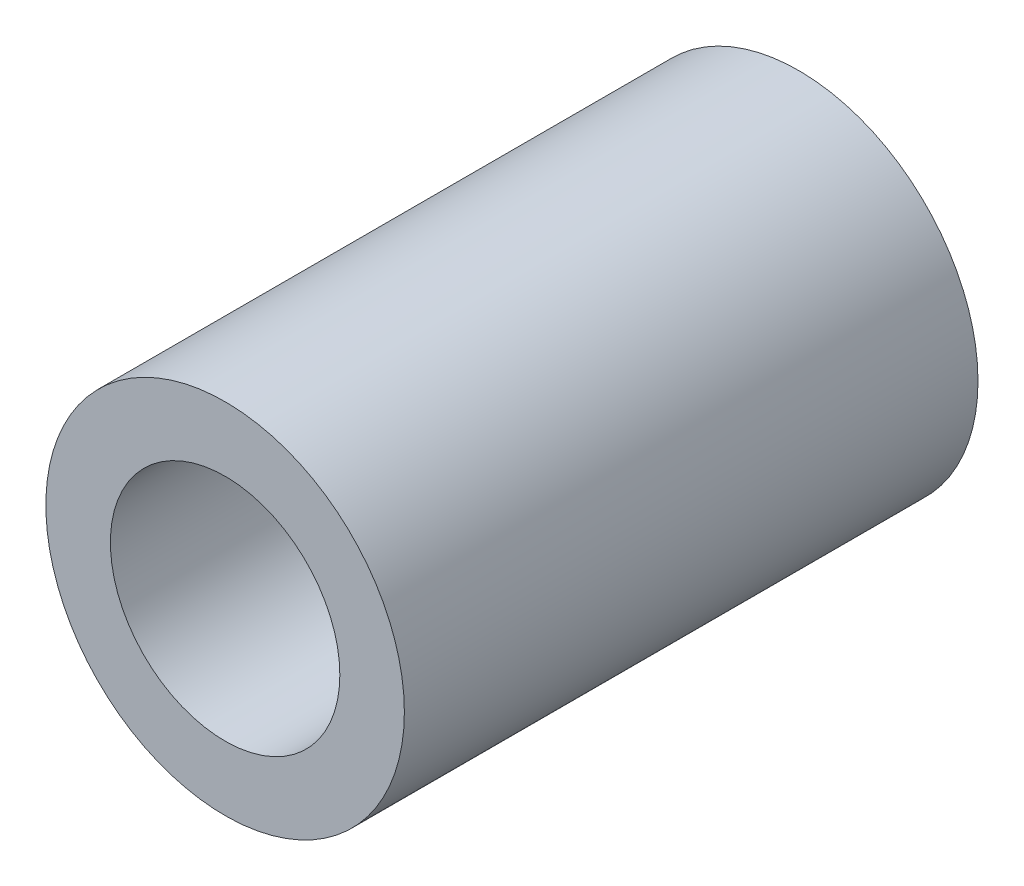
SolidWorks part; units mm, degrees
material "ABS"
ref_plane "前视基准面" through (0, 0, 0) normal (0, 0, 1) x (1, 0, 0)
ref_plane "上视基准面" through (0, 0, 0) normal (0, 1, 0) x (1, 0, 0)
ref_plane "右视基准面" through (0, 0, 0) normal (1, 0, 0) x (0, 0, -1)
sketch "草图1" plane through (0, 0, 0) normal (0, 0, 1) x (1, 0, 0)
  circle A0 centre (0, 0) radius 2.5
  circle A1 centre (0, 0) radius 1.6
  dimension "D1" = 5
  dimension "D2" = 3.2
extrude "凸台-拉伸1" add sketch "草图1" along normal blind 8
